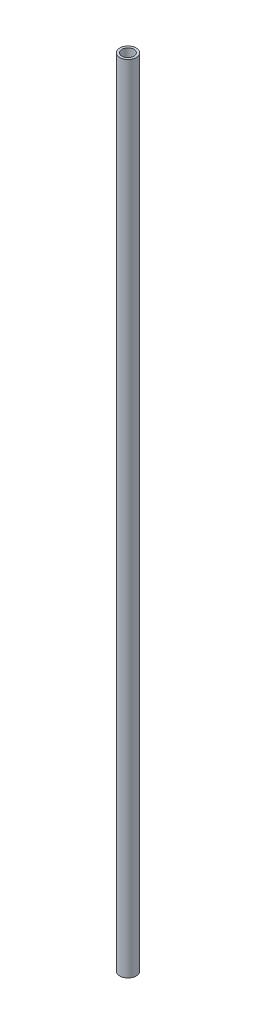
SolidWorks part; units mm, degrees
material "AISI 304"
ref_plane "Front Plane" through (0, 0, 0) normal (0, 0, 1) x (1, 0, 0)
ref_plane "Top Plane" through (0, 0, 0) normal (0, 1, 0) x (1, 0, 0)
ref_plane "Right Plane" through (0, 0, 0) normal (1, 0, 0) x (0, 0, -1)
sketch "Sketch1" plane through (0, 0, 0) normal (0, 1, 0) x (1, 0, 0)
  circle A0 centre (0, 0) radius 3.175
  circle A1 centre (0, 0) radius 2.286
  dimension "D1" = 6.35
  dimension "D2" = 4.572
extrude "Boss-Extrude1" add sketch "Sketch1" along normal blind 304.8
